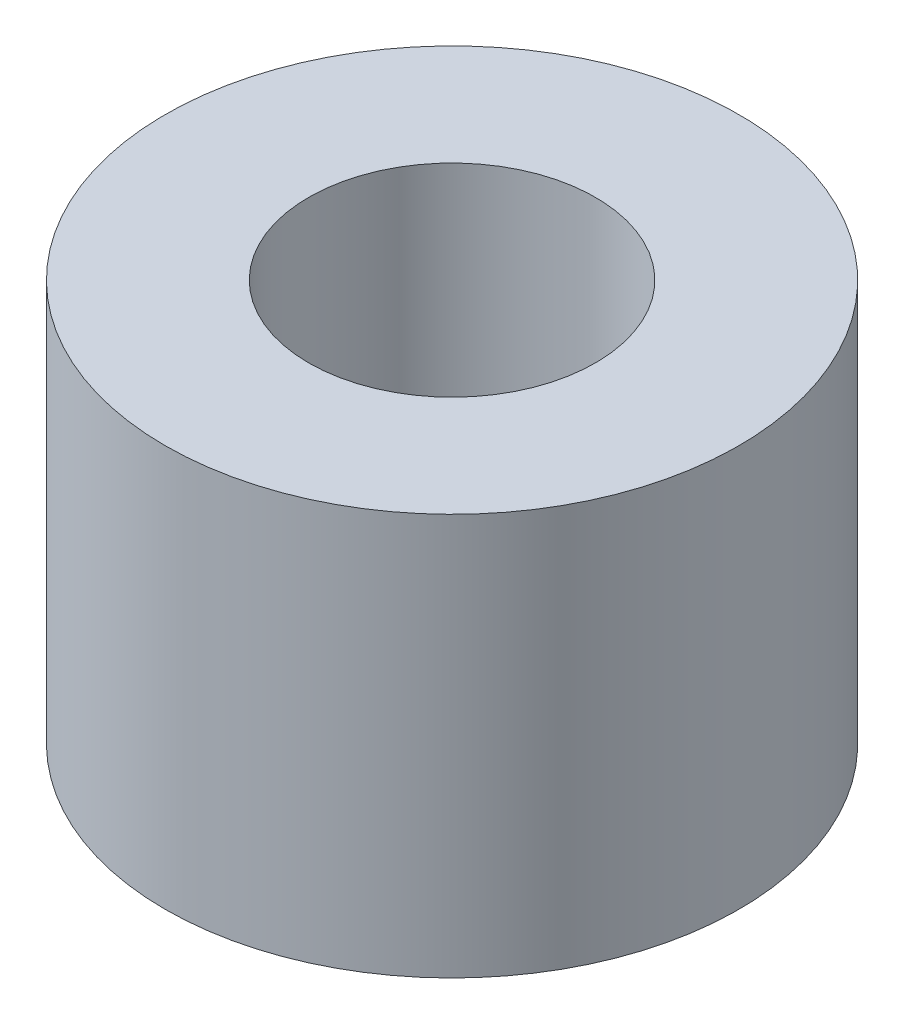
SolidWorks part; units mm, degrees
ref_plane "Спереди" through (0, 0, 0) normal (0, 0, 1) x (1, 0, 0)
ref_plane "Сверху" through (0, 0, 0) normal (0, 1, 0) x (1, 0, 0)
ref_plane "Справа" through (0, 0, 0) normal (1, 0, 0) x (0, 0, -1)
sketch "Эскиз1" plane through (0, 0, 0) normal (0, 1, 0) x (1, 0, 0)
  circle A0 centre (0, 0) radius 5
  circle A1 centre (0, 0) radius 2.5
extrude "Бобышка-Вытянуть1" add sketch "Эскиз1" along normal blind 7
